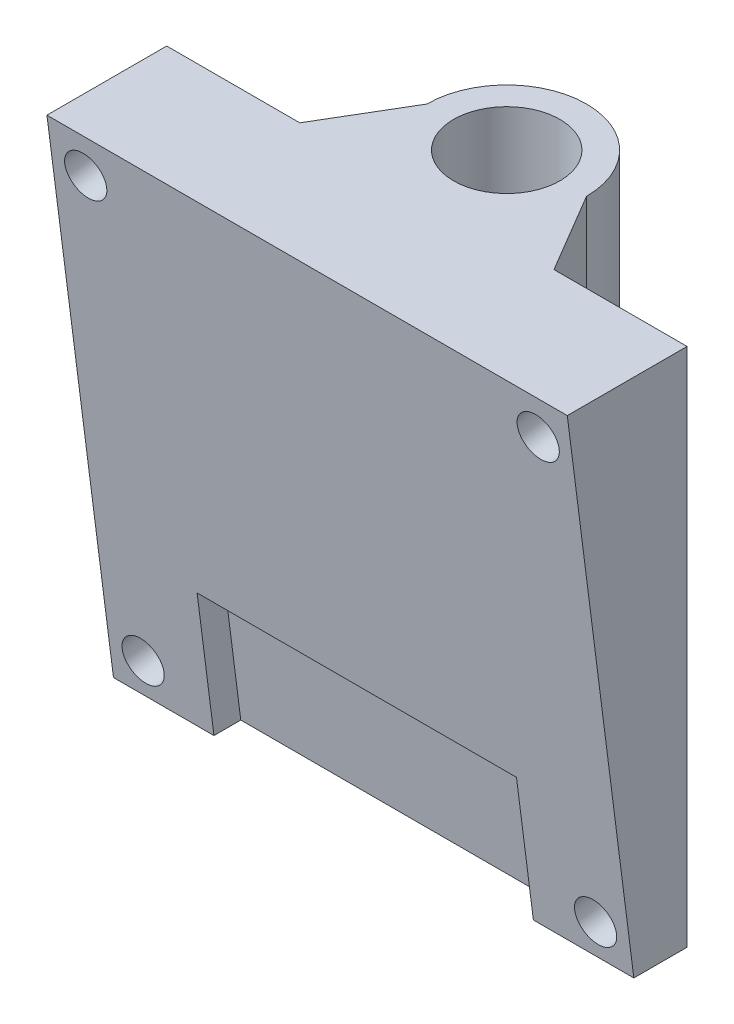
SolidWorks part; units mm, degrees
ref_plane "Спереди" through (0, 0, 0) normal (0, 0, 1) x (1, 0, 0)
ref_plane "Сверху" through (0, 0, 0) normal (0, 1, 0) x (1, 0, 0)
ref_plane "Справа" through (0, 0, 0) normal (1, 0, 0) x (0, 0, -1)
sketch "Эскиз1" plane through (0, 0, 0) normal (0, 1, 0) x (1, 0, 0)
  line L0 (0, 0) -> (0, -20) construction
  line L1 (-19.55, -10) -> (19.55, -10)
  line L2 (-19.55, -10) -> (-19.55, -6)
  line L4 (19.55, -10) -> (19.55, -6)
  line L6 (-19.55, -6) -> (-9.55, -6)
  line L7 (-9.55, -6) -> (-6, 0)
  line L8 (19.55, -6) -> (9.55, -6)
  line L9 (9.55, -6) -> (6, 0)
  circle A0 centre (0, 0) radius 4
  arc A1 (6, 0) -> (-6, 0) centre (0, 0) ccw
  point P7 (0, -10)
  dimension "D1" = 8
  dimension "D2" = 12
  dimension "D3" = 39.1
  dimension "D4" = 10
  dimension "D5" = 4
  dimension "D6" = 4
  dimension "D7" = 10
  dimension "D8" = 10
extrude "Бобышка-Вытянуть1" add sketch "Эскиз1" along normal blind 39.1
sketch "Эскиз5" plane through (19.55, 0, 0) normal (1, 0, 0) x (0, 0, -1)
  line L0 (-10, 0) -> (-15, 39.1)
  line L1 (-15, 39.1) -> (-10, 39.1)
  line L2 (-10, 39.1) -> (-10, 0)
  dimension "D1" = 5
extrude "Бобышка-Вытянуть2" add sketch "Эскиз5" against normal up to vertex (39.1 mm away)
hole_wizard "Сверло под метчик  спиральное M32" positions "Эскиз8" profile "Эскиз9" hole size "M3x0.5" standard "DIN" end condition through all
sketch "Эскиз8" plane through (0, -1.2582, 9.8391) normal (0, -0.1268, 0.9919) x (1, 0, 0)
  line L0 (-19.55, 1.2684) -> (19.55, 1.2684) construction
  line L1 (-19.55, 40.6868) -> (-19.55, 1.2684) construction
  point P0 (-17, 3.8184)
  dimension "D1" = 2.55
  dimension "D2" = 2.55
sketch "Эскиз9" plane through (-17, 2.5294, 10.3235) normal (1, 0, 0) x (0, -0.9919, -0.1268)
  line L0 (0, 0) -> (0, 20.8304)
  line L1 (0, 20.8304) -> (1.575, 20.8304)
  line L2 (1.575, 20.8304) -> (1.575, 0)
  line L5 (1.575, 0) -> (0, 0)
  line L11 (0, -6.35) -> (0, 107.95) construction
  dimension "Диаметр сквозного отверстия" = 3.15
  dimension "Глубина сквозного отверстия" = 20.8304
pattern_linear "Линейный массив2" count 2 spacing 34 along (1, 0, 0) count 2 spacing 34 along (0, 0.9919, 0.1268) of "Сверло под метчик  спиральное M32"
sketch "Эскиз10" plane through (0, -1.2582, 9.8391) normal (0, -0.1268, 0.9919) x (1, 0, 0)
  line L0 (0, 0) -> (0, 20.4179) construction
  line L1 (-12, -0.7316) -> (-12, 11.2684)
  line L2 (-12, 11.2684) -> (12, 11.2684)
  line L3 (12, 11.2684) -> (12, -0.7316)
  line L4 (12, -0.7316) -> (-12, -0.7316)
  line L6 (-19.55, 1.2684) -> (19.55, 1.2684) construction
  dimension "D1" = 24
  dimension "D2" = 12
  dimension "D3" = 10
  dimension "D4" = 12
extrude "Вырез-Вытянуть2" cut sketch "Эскиз10" against normal blind 2
